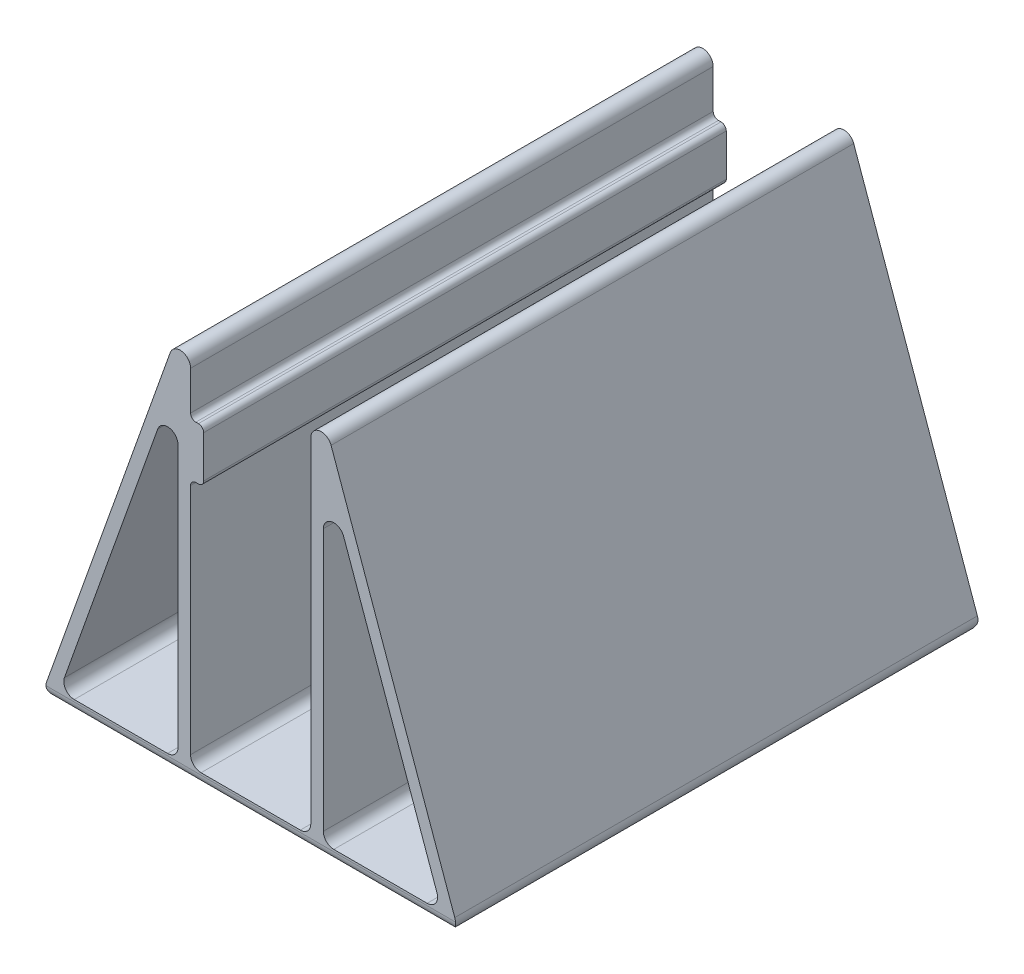
SolidWorks part; units mm, degrees
ref_plane "Plan de face" through (0, 0, 0) normal (0, 0, 1) x (1, 0, 0)
ref_plane "Plan de dessus" through (0, 0, 0) normal (0, 1, 0) x (1, 0, 0)
ref_plane "Plan de droite" through (0, 0, 0) normal (1, 0, 0) x (0, 0, -1)
sketch "Esquisse1" plane through (0, 0, 0) normal (0, 0, 1) x (1, 0, 0)
  line L0 (-11.5, 2.4) -> (11.5, 2.4)
  line L1 (11.5, 2.4) -> (11.5, 80)
  line L2 (11.5, 80) -> (40, 0)
  line L3 (40, 0) -> (-40, 0)
  line L4 (0, 0) -> (0, 138.9113) construction
  line L5 (-11.5, 2.4) -> (-11.5, 50)
  line L6 (-11.5, 80) -> (-40, 0)
  line L7 (-11.5, 50) -> (-9, 50)
  line L8 (-9, 50) -> (-9, 60)
  line L9 (-9, 60) -> (-11.5, 60)
  line L10 (-11.5, 60) -> (-11.5, 80)
  line L11 (13.9, 66.1116) -> (13.9, 2.4)
  line L12 (13.9, 2.4) -> (36.5973, 2.4)
  line L13 (36.5973, 2.4) -> (13.9, 66.1116)
  line L14 (-13.9, 2.4) -> (-36.5973, 2.4)
  line L15 (-13.9, 66.1116) -> (-13.9, 2.4)
  line L16 (-36.5973, 2.4) -> (-13.9, 66.1116)
  point P3 (0, 2.4)
  dimension "D1" = 23
  dimension "D2" = 80
  dimension "D3" = 80
  dimension "D4" = 2.4
  dimension "D5" = 2.5
  dimension "D6" = 10
  dimension "D7" = 20
  dimension "D8" = 2.4
  dimension "D9" = 2.4
  dimension "D10" = 2.4
extrude "Boss.-Extru.1" add sketch "Esquisse1" along normal blind 100
fillet "Congé1" radius 2 14 edges at (0, 0, 0) (0, 0, 100) (11.5, 80, 50) (-40, 0, 50) (40, 0, 50) (11.5, 2.4, 50) (-11.5, 2.4, 50) (-11.5, 80, 50) (13.9, 66.1116, 50) (36.5973, 2.4, 50) (13.9, 2.4, 50) (-13.9, 2.4, 50) (-36.5973, 2.4, 50) (-13.9, 66.1116, 50)
fillet "Congé2" radius 1 4 edges at (-11.5, 60, 50) (-9, 60, 50) (-9, 50, 50) (-11.5, 50, 50)
equation "\"ep\"= 2.4"
equation "\"D4@Esquisse1\"=\"ep\""
equation "\"D9@Esquisse1\"=\"ep\""
equation "\"D10@Esquisse1\"=\"ep\""
equation "\"D8@Esquisse1\"=\"ep\""
